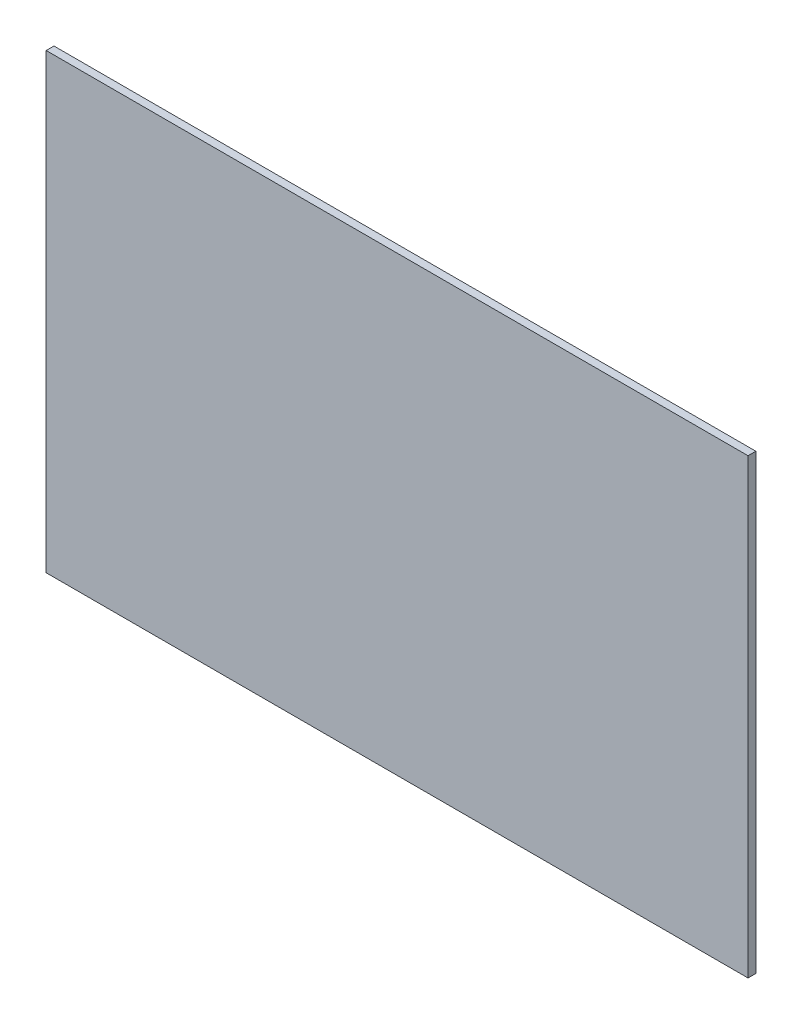
SolidWorks part; units mm, degrees
material "Glass"
ref_plane "Front Plane" through (0, 0, 0) normal (0, 0, 1) x (1, 0, 0)
ref_plane "Top Plane" through (0, 0, 0) normal (0, 1, 0) x (1, 0, 0)
ref_plane "Right Plane" through (0, 0, 0) normal (1, 0, 0) x (0, 0, -1)
sketch "Sketch1" plane through (0, 0, 0) normal (0, 0, 1) x (1, 0, 0)
  line L1 (-285.75, 184.15) -> (285.75, 184.15)
  line L2 (-285.75, 184.15) -> (-285.75, -184.15)
  line L3 (-285.75, -184.15) -> (285.75, -184.15)
  line L4 (285.75, 184.15) -> (285.75, -184.15)
  line L5 (-285.75, 184.15) -> (285.75, -184.15) construction
  line L6 (-285.75, -184.15) -> (285.75, 184.15) construction
  point P0 (0, 0)
  dimension "D1" = 368.3
  dimension "D2" = 571.5
extrude "Boss-Extrude1" add sketch "Sketch1" along normal blind 6.35
